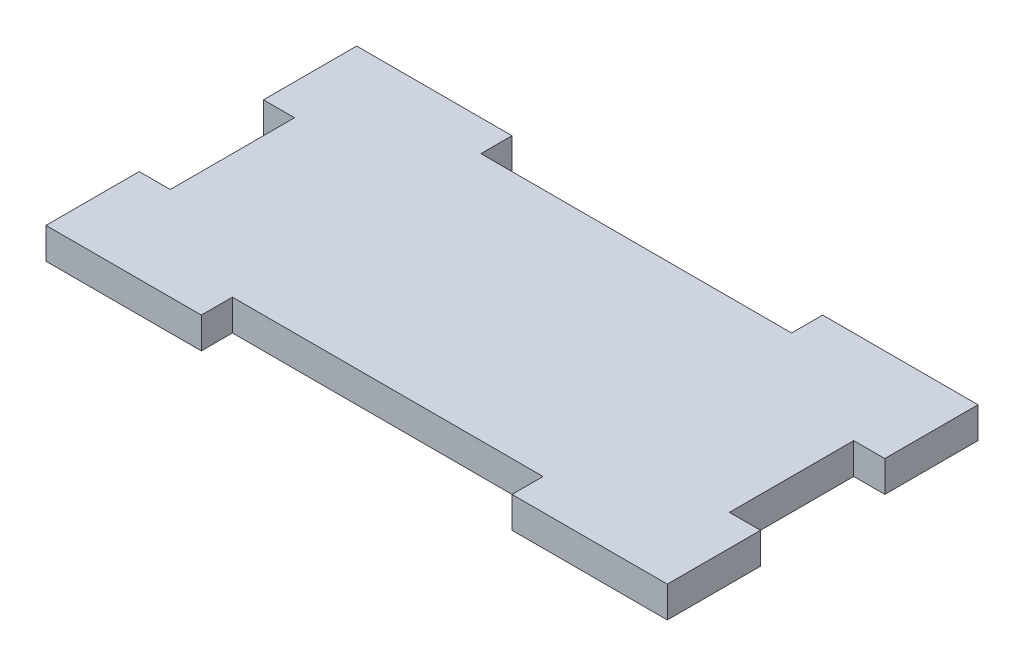
SolidWorks part; units mm, degrees
ref_plane "Front Plane" through (0, 0, 0) normal (0, 0, 1) x (1, 0, 0)
ref_plane "Top Plane" through (0, 0, 0) normal (0, 1, 0) x (1, 0, 0)
ref_plane "Right Plane" through (0, 0, 0) normal (1, 0, 0) x (0, 0, -1)
sketch "Sketch1" plane through (0, 0, 0) normal (0, 1, 0) x (1, 0, 0)
  line L1 (-50, -9.0152) -> (-50, -24.0152)
  line L2 (-50, 25.9848) -> (-25, 25.9848)
  line L3 (-50, 25.9848) -> (-50, 10.9848)
  line L4 (-50, -24.0152) -> (-25, -24.0152)
  line L5 (50, 25.9848) -> (50, 10.9848)
  line L8 (-25, 25.9848) -> (-25, 20.9848)
  line L9 (-25, 20.9848) -> (25, 20.9848)
  line L10 (25, 20.9848) -> (25, 25.9848)
  line L11 (-25, -24.0152) -> (-25, -19.0152)
  line L12 (-25, -19.0152) -> (25, -19.0152)
  line L13 (25, -19.0152) -> (25, -24.0152)
  line L14 (50, 10.9848) -> (45, 10.9848)
  line L15 (45, 10.9848) -> (45, -9.0152)
  line L16 (45, -9.0152) -> (50, -9.0152)
  line L17 (-50, 10.9848) -> (-45, 10.9848)
  line L18 (-45, 10.9848) -> (-45, -9.0152)
  line L19 (-45, -9.0152) -> (-50, -9.0152)
  line L20 (25, 25.9848) -> (50, 25.9848)
  line L22 (-45, 0.9848) -> (45, 0.9848) construction
  line L23 (25, -24.0152) -> (50, -24.0152)
  line L24 (50, -9.0152) -> (50, -24.0152)
  point P3 (0, 0)
  dimension "D1" = 100
  dimension "D2" = 50
  dimension "D3" = 5
  dimension "D4" = 50
  dimension "D5" = 5
  dimension "D6" = 20
  dimension "D7" = 5
  dimension "D8" = 5
  dimension "D9" = 20
  dimension "D10" = 15
  dimension "D11" = 25
  dimension "D12" = 25
extrude "Boss-Extrude1" add sketch "Sketch1" along normal blind 5
